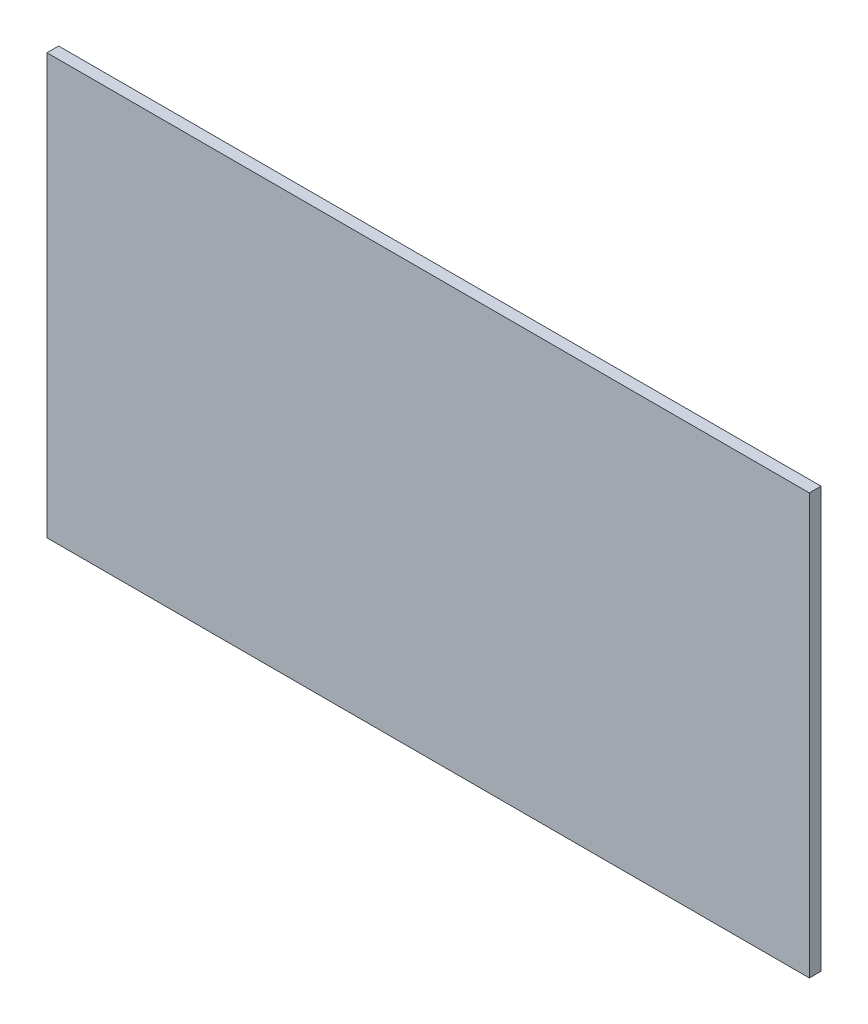
SolidWorks part; units mm, degrees
ref_plane "Front Plane" through (0, 0, 0) normal (0, 0, 1) x (1, 0, 0)
ref_plane "Top Plane" through (0, 0, 0) normal (0, 1, 0) x (1, 0, 0)
ref_plane "Right Plane" through (0, 0, 0) normal (1, 0, 0) x (0, 0, -1)
sketch "Sketch1" plane through (0, 0, 0) normal (0, 0, 1) x (1, 0, 0)
  line L1 (0, 0) -> (196, 0)
  line L2 (0, 0) -> (0, 108)
  line L3 (0, 108) -> (196, 108)
  line L4 (196, 0) -> (196, 108)
  dimension "D1" = 108
  dimension "D2" = 196
extrude "Boss-Extrude1" add sketch "Sketch1" along normal blind 3
